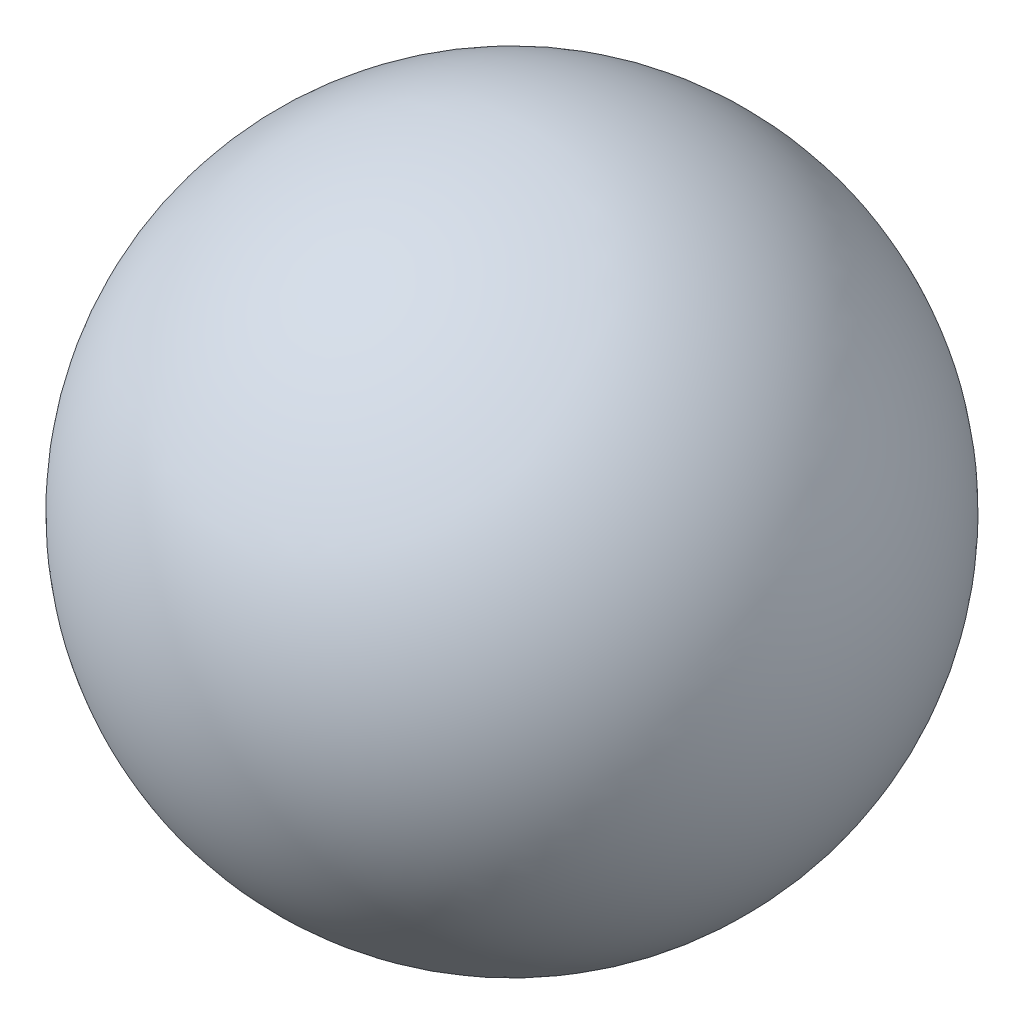
SolidWorks part; units mm, degrees
ref_plane "前视基准面" through (0, 0, 0) normal (0, 0, 1) x (1, 0, 0)
ref_plane "上视基准面" through (0, 0, 0) normal (0, 1, 0) x (1, 0, 0)
ref_plane "右视基准面" through (0, 0, 0) normal (1, 0, 0) x (0, 0, -1)
sketch "草图1" plane through (0, 0, 0) normal (0, 1, 0) x (1, 0, 0)
  line L0 (0, 15) -> (0, -15)
  arc A0 (0, 15) -> (0, -15) centre (0, 0) ccw
revolve "旋转1" add sketch "草图1" angle 360 about L0
